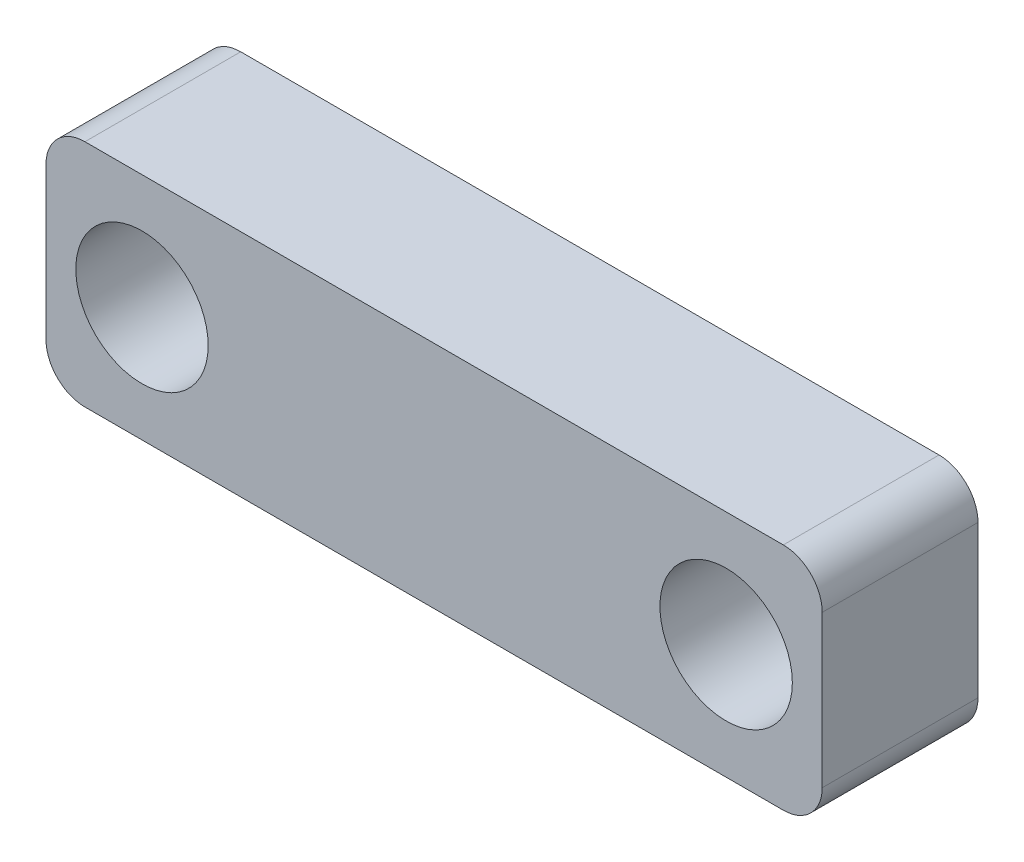
SolidWorks part; units mm, degrees
ref_plane "Plano frontal" through (0, 0, 0) normal (0, 0, 1) x (1, 0, 0)
ref_plane "Plano superior" through (0, 0, 0) normal (0, 1, 0) x (1, 0, 0)
ref_plane "Plano direito" through (0, 0, 0) normal (1, 0, 0) x (0, 0, -1)
ref_plane "Plane1" through (0, 0, 133.3657) normal (0, 0, 1) x (1, 0, 0)
sketch "Sketch2" plane through (0, 0, 133.3657) normal (0, 0, 1) x (1, 0, 0)
  line L1 (-31.2221, 40.9398) -> (-11.2895, 40.9398)
  line L2 (-31.2221, 40.9398) -> (-31.2221, 35.0398)
  line L3 (-31.2221, 35.0398) -> (-11.2895, 35.0398)
  line L4 (-11.2895, 40.9398) -> (-11.2895, 35.0398)
  dimension "D1" = 5.9
extrude "Boss-Extrude1" add sketch "Sketch2" along normal blind 4
fillet "Fillet1" radius 1 4 edges at (-11.2895, 35.0398, 135.3657) (-11.2895, 40.9398, 135.3657) (-31.2221, 35.0398, 135.3657) (-31.2221, 40.9398, 135.3657)
hole_wizard "M3 Clearance Hole1" positions "Sketch5" profile "Sketch3" hole size "M3" standard "ISO"
sketch "Sketch5" plane through (0, 0, 137.3657) normal (0, 0, 1) x (1, 0, 0)
  line L0 (-12.2895, 40.9398) -> (-30.2221, 40.9398) construction
  line L1 (-31.2221, 39.9398) -> (-31.2221, 36.0398) construction
  point P0 (-28.7571, 37.9898)
  point P2 (-13.7571, 37.9898)
  dimension "D1" = 2.95
  dimension "D2" = 2.95
  dimension "D3" = 15
  dimension "D4" = 2.465
sketch "Sketch3" plane through (-28.7571, 37.9898, 137.3657) normal (1, 0, 0) x (0, -1, 0)
  line L0 (0, 0) -> (0, 17.5215)
  line L1 (0, 17.5215) -> (1.7, 16.5)
  line L2 (1.7, 16.5) -> (1.7, 0)
  line L5 (1.7, 0) -> (0, 0)
  line L10 (0, 17.5215) -> (-1.7, 16.5) construction
  line L11 (0, -6.35) -> (0, 107.95) construction
  dimension "Hole Dia." = 3.4
  dimension "Hole Depth" = 16.5
  dimension "Drill Angle" = 118
